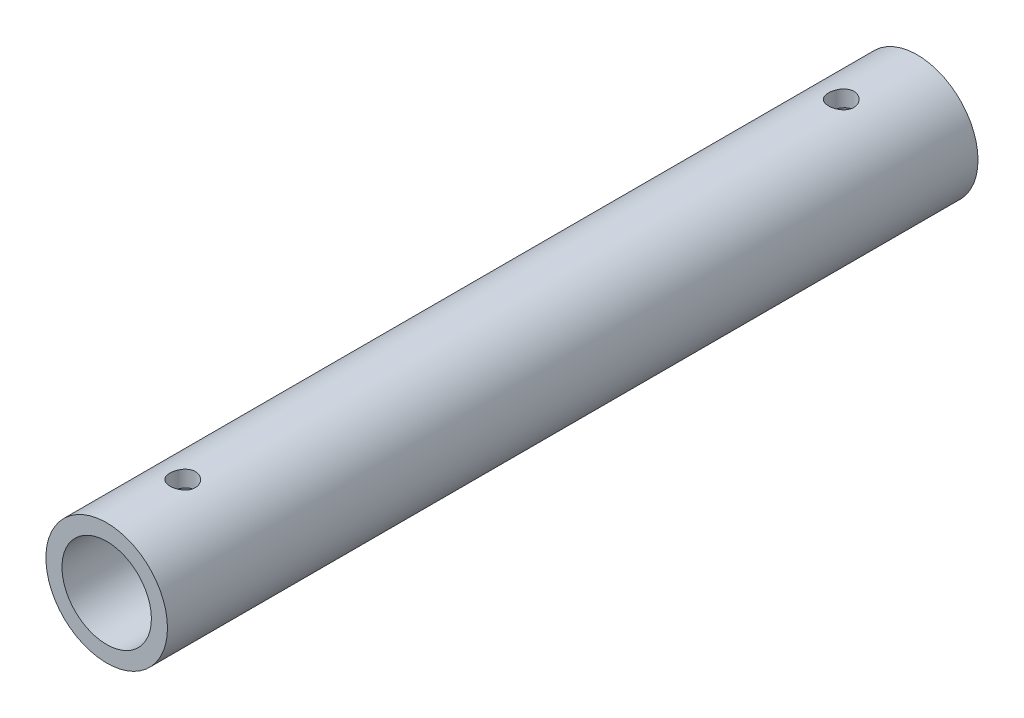
SolidWorks part; units mm, degrees
material "1060 Alloy"
ref_plane "Front Plane" through (0, 0, 0) normal (0, 0, 1) x (1, 0, 0)
ref_plane "Top Plane" through (0, 0, 0) normal (0, 1, 0) x (1, 0, 0)
ref_plane "Right Plane" through (0, 0, 0) normal (1, 0, 0) x (0, 0, -1)
sketch "Sketch1" plane through (0, 0, 0) normal (0, 0, 1) x (1, 0, 0)
  circle A0 centre (0, 0) radius 12
  dimension "D1" = 24
extrude "Boss-Extrude1" add sketch "Sketch1" along normal blind 160
shell "Shell1" thickness 3.175
sketch "Sketch2" plane through (0, 0, 0) normal (0, 1, 0) x (1, 0, 0)
  line L0 (0, 0) -> (0, -15) construction
  line L1 (0, -160) -> (0, -145) construction
  line L2 (-12, -160) -> (12, -160) construction
  circle A0 centre (0, -15) radius 2.5
  circle A1 centre (0, -145) radius 2.5
  dimension "D2" = 5
  dimension "D1" = 15
extrude "Cut-Extrude1" cut sketch "Sketch2" against normal through all both and the other way through all
equation "\"tubeOutDiameter\" = 35mm"
equation "\"wheelShaftDiameter\"= 12mm"
equation "\"wheelThickness\"= 135mm"
equation "\"BearingDiameter\"= 20mm"
equation "\"BearingThickness\"= 10mm"
equation "\"frontShaftDiameter\"= 20mm"
equation "\"D1@Sketch1\"=\"wheelShaftDiameter\"*2"
